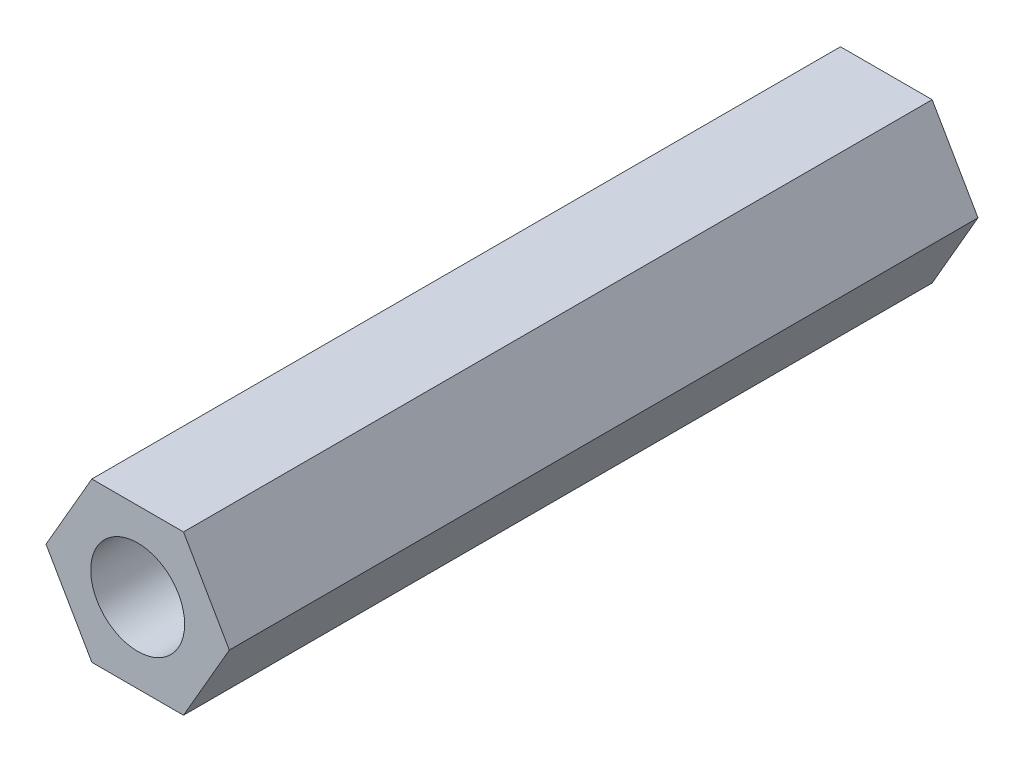
SolidWorks part; units mm, degrees
ref_plane "Front Plane" through (0, 0, 0) normal (0, 0, 1) x (1, 0, 0)
ref_plane "Top Plane" through (0, 0, 0) normal (0, 1, 0) x (1, 0, 0)
ref_plane "Right Plane" through (0, 0, 0) normal (1, 0, 0) x (0, 0, -1)
sketch "Sketch1" plane through (0, 0, 0) normal (0, 0, 1) x (1, 0, 0)
  line L1 (2.6229, 106.889) -> (1.259, 104.5268)
  line L2 (1.259, 104.5268) -> (2.6229, 102.1646)
  line L3 (2.6229, 102.1646) -> (5.3505, 102.1646)
  line L4 (5.3505, 102.1646) -> (6.7143, 104.5268)
  line L5 (6.7143, 104.5268) -> (5.3505, 106.889)
  line L6 (5.3505, 106.889) -> (2.6229, 106.889)
  circle A0 centre (3.9867, 104.5268) radius 2.3622 construction
  circle A1 centre (3.9867, 104.5268) radius 1.397 construction
  circle A2 centre (3.9867, 104.5268) radius 1.397
  dimension "D1" = 4.7244
extrude "Boss-Extrude1" add sketch "Sketch1" along normal blind 22.2758
